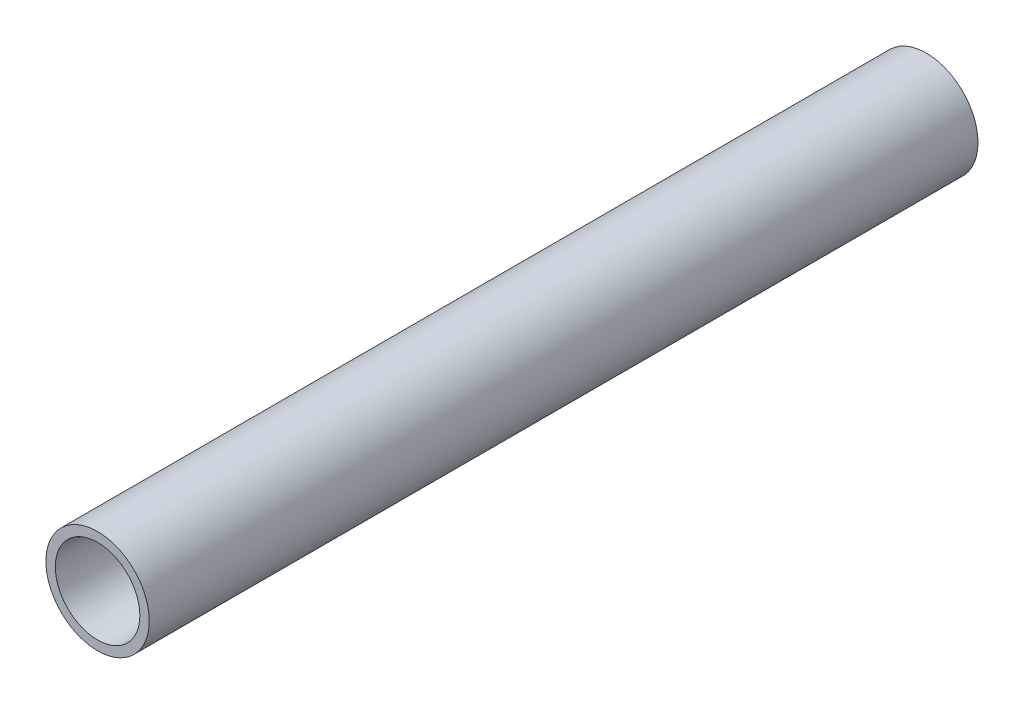
SolidWorks part; units mm, degrees
ref_plane "Front Plane" through (0, 0, 0) normal (0, 0, 1) x (1, 0, 0)
ref_plane "Top Plane" through (0, 0, 0) normal (0, 1, 0) x (1, 0, 0)
ref_plane "Right Plane" through (0, 0, 0) normal (1, 0, 0) x (0, 0, -1)
sketch "Sketch1" plane through (0, 0, 0) normal (0, 0, 1) x (1, 0, 0)
  circle A0 centre (0, 0) radius 2.775
  dimension "D1" = 5.55
extrude "Boss-Extrude1" add sketch "Sketch1" along normal blind 44.5
sketch "Sketch2" plane through (0, 0, 0) normal (0, 0, 1) x (1, 0, 0)
  circle A0 centre (0, 0) radius 2.27
  dimension "D1" = 4.54
extrude "Cut-Extrude1" cut sketch "Sketch2" along a picked direction on the side of the normal blind 5.68 draft 3.074
sketch "Sketch7" plane through (0, 0, 0) normal (0, 0, 1) x (1, 0, 0)
  circle A0 centre (0, 0) radius 1
extrude "Cut-Extrude2" cut sketch "Sketch7" along normal through all
sketch "Sketch9" plane through (0, 0, 44.5) normal (0, 0, 1) x (1, 0, 0)
  circle A0 centre (0, 0) radius 2.27
  circle A1 centre (0, 0) radius 2.27 construction
extrude "Cut-Extrude3" cut sketch "Sketch9" against normal blind 5.68 draft 3.074
